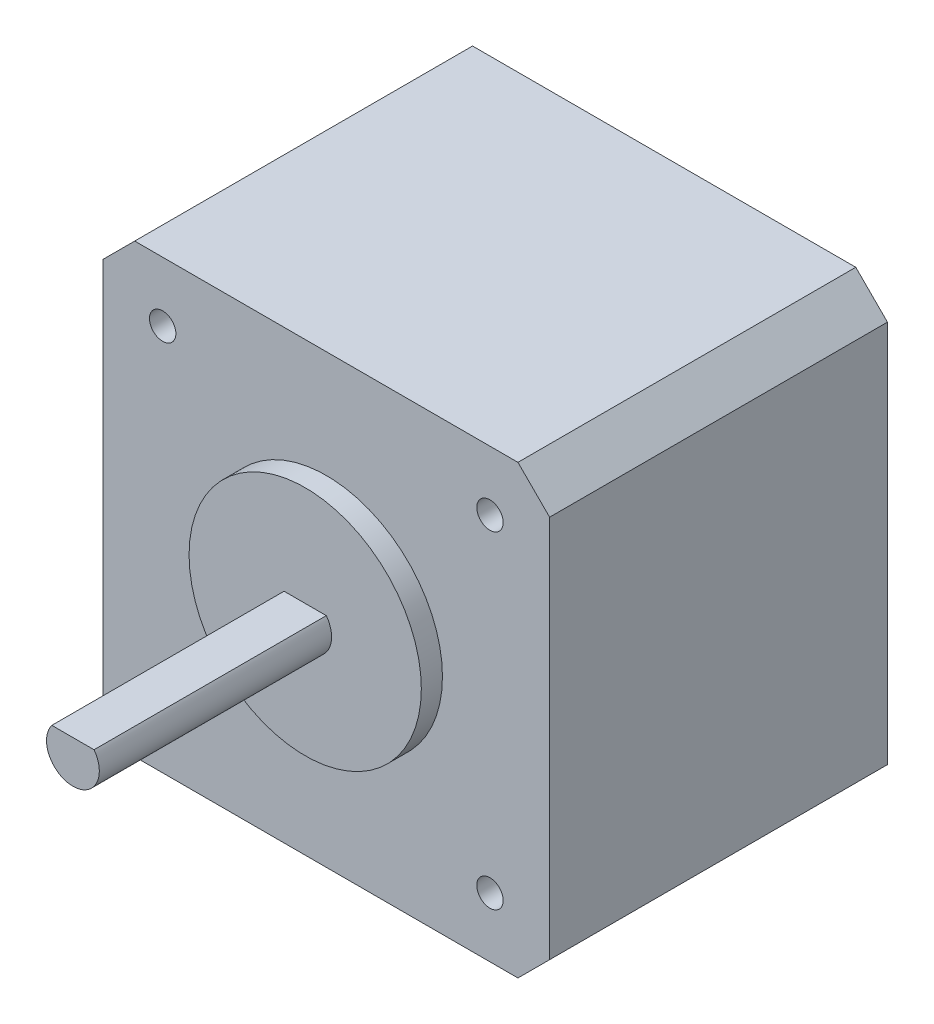
SolidWorks part; units mm, degrees
ref_plane "Plan de face" through (0, 0, 0) normal (0, 0, 1) x (1, 0, 0)
ref_plane "Plan de dessus" through (0, 0, 0) normal (0, 1, 0) x (1, 0, 0)
ref_plane "Plan de droite" through (0, 0, 0) normal (1, 0, 0) x (0, 0, -1)
sketch "Esquisse1" plane through (0, 0, 0) normal (0, 0, 1) x (1, 0, 0)
  line L0 (21.15, 18.15) -> (18.15, 21.15)
  line L1 (18.15, 21.15) -> (-18.15, 21.15)
  line L2 (21.15, 18.15) -> (21.15, -18.15)
  line L3 (18.15, -21.15) -> (-18.15, -21.15)
  line L4 (-21.15, 18.15) -> (-21.15, -18.15)
  line L5 (21.15, 21.15) -> (-21.15, -21.15) construction
  line L6 (21.15, -21.15) -> (-21.15, 21.15) construction
  line L7 (-18.15, 21.15) -> (-21.15, 18.15)
  line L8 (-18.15, -21.15) -> (-21.15, -18.15)
  line L9 (21.15, -18.15) -> (18.15, -21.15)
  point P0 (0, 0)
  dimension "D1" = 42.3
  dimension "D2" = 42.3
extrude "Boss.-Extru.1" add sketch "Esquisse1" along normal blind 32
sketch "Esquisse2" plane through (0, 0, 32) normal (0, 0, 1) x (1, 0, 0)
  circle A0 centre (0, 0) radius 11
  dimension "D1" = 22
extrude "Boss.-Extru.2" add sketch "Esquisse2" along normal blind 2
sketch "Esquisse3" plane through (0, 0, 34) normal (0, 0, 1) x (1, 0, 0)
  line L0 (-2, 1.5) -> (2, 1.5)
  arc A0 (-2, 1.5) -> (2, 1.5) centre (0, 0) ccw
  dimension "D1" = 5
  dimension "D2" = 1.5
extrude "Boss.-Extru.3" add sketch "Esquisse3" along normal blind 22
sketch "Esquisse4" plane through (0, 0, 32) normal (0, 0, 1) x (1, 0, 0)
  line L5 (15.5, 15.5) -> (-15.5, 15.5) construction
  line L6 (15.5, 15.5) -> (15.5, -15.5) construction
  line L7 (15.5, -15.5) -> (-15.5, -15.5) construction
  line L8 (-15.5, 15.5) -> (-15.5, -15.5) construction
  line L9 (15.5, 15.5) -> (-15.5, -15.5) construction
  line L10 (15.5, -15.5) -> (-15.5, 15.5) construction
  circle A0 centre (-15.5, 15.5) radius 1.25
  circle A1 centre (15.5, 15.5) radius 1.25
  circle A2 centre (15.5, -15.5) radius 1.25
  circle A3 centre (-15.5, -15.5) radius 1.25
  point P8 (0, 0)
  point P9 (0, 0)
  point P10 (0, 0)
  point P11 (0, 0)
  point P16 (0, 0)
  dimension "D1" = 2.5
  dimension "D10" = 31
  dimension "D11" = 31
extrude "Enlèv. mat.-Extru.1" cut sketch "Esquisse4" against normal blind 10
